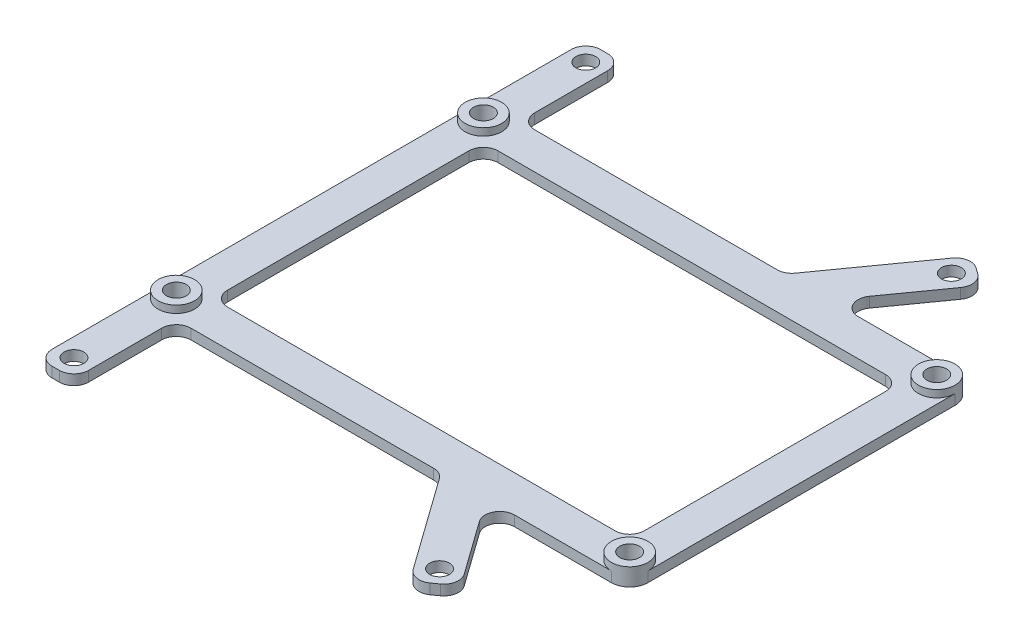
SolidWorks part; units mm, degrees
ref_plane "Front Plane" through (0, 0, 0) normal (0, 0, 1) x (1, 0, 0)
ref_plane "Top Plane" through (0, 0, 0) normal (0, 1, 0) x (1, 0, 0)
ref_plane "Right Plane" through (0, 0, 0) normal (1, 0, 0) x (0, 0, -1)
sketch "Sketch1" plane through (0, 0, 0) normal (0, 1, 0) x (1, 0, 0)
  line L0 (6, 0) -> (0, 0) construction
  line L1 (-25, -35) -> (25, -35) construction
  line L2 (-25, -35) -> (-25, 35) construction
  line L3 (-25, 35) -> (25, 35) construction
  line L4 (25, -35) -> (25, 35) construction
  line L5 (-25, -35) -> (25, 35) construction
  line L6 (-25, 35) -> (25, -35) construction
  line L7 (-25, -21) -> (37, -21) construction
  line L8 (-25, -21) -> (-25, 21) construction
  line L9 (-25, 21) -> (37, 21) construction
  line L10 (37, -21) -> (37, 21) construction
  line L11 (-25, -21) -> (37, 21) construction
  line L12 (-25, 21) -> (37, -21) construction
  circle A0 centre (-25, 35) radius 1.35
  circle A1 centre (25, 35) radius 1.35
  circle A2 centre (25, -35) radius 1.35
  circle A3 centre (-25, -35) radius 1.35
  circle A4 centre (-25, 21) radius 1.35
  circle A5 centre (37, 21) radius 1.35
  circle A6 centre (37, -21) radius 1.35
  circle A7 centre (-25, -21) radius 1.35
  point P0 (0, 0)
  point P10 (6, 0)
  dimension "D1" = 2.7
  dimension "D6" = 2.7
  dimension "D2" = 70
  dimension "D3" = 50
  dimension "D4" = 42
  dimension "D5" = 62
  dimension "D7" = 6
sketch "Sketch2" plane through (0, 0, 0) normal (0, 1, 0) x (1, 0, 0)
  line L0 (0, 0) -> (50000, 0) construction
  line L1 (-27.5, -37.5) -> (-27.5, 37.5)
  line L2 (-27.5, 37.5) -> (-22.5, 37.5)
  line L3 (-22.5, 37.5) -> (-22.5, 23.5)
  line L4 (-22.5, 23.5) -> (13.7135, 23.5)
  line L5 (13.7135, 23.5) -> (24.4188, 38.4874)
  line L6 (24.4188, 38.4874) -> (28.4874, 35.5812)
  line L7 (28.4874, 35.5812) -> (19.858, 23.5)
  line L8 (19.858, 23.5) -> (39.5, 23.5)
  line L9 (39.5, 23.5) -> (39.5, -23.5)
  line L10 (34.5, -18.5) -> (34.5, 18.5)
  line L11 (34.5, 18.5) -> (-22.5, 18.5)
  line L12 (-22.5, 18.5) -> (-22.5, -18.5)
  line L13 (-25, -35) -> (-25, 35) construction
  line L14 (-25, 21) -> (37, 21) construction
  line L15 (37, -21) -> (37, 21) construction
  line L16 (-25, -35) -> (25, 35) construction
  line L17 (34.5, -18.5) -> (-22.5, -18.5)
  line L18 (19.858, -23.5) -> (39.5, -23.5)
  line L19 (28.4874, -35.5812) -> (19.858, -23.5)
  line L20 (24.4188, -38.4874) -> (28.4874, -35.5812)
  line L21 (13.7135, -23.5) -> (24.4188, -38.4874)
  line L22 (-22.5, -23.5) -> (13.7135, -23.5)
  line L23 (-22.5, -37.5) -> (-22.5, -23.5)
  line L24 (-27.5, -37.5) -> (-22.5, -37.5)
  point P28 (39.5, 0)
  point P29 (34.5, 0)
  point P30 (-22.5, 0)
  point P31 (-27.5, 0)
  dimension "D1" = 2.5
  dimension "D2" = 2.5
  dimension "D3" = 2.5
  dimension "D4" = 2.5
  dimension "D5" = 2.5
  dimension "D6" = 2.5
  dimension "D7" = 2.5
  dimension "D8" = 2.5
  dimension "D9" = 2.5
  dimension "D10" = 2.5
extrude "Boss-Extrude1" add sketch "Sketch2" along normal blind 1.4
extrude "Cut-Extrude2" cut sketch "Sketch1" along normal through all
fillet "Fillet1" radius 2 8 edges at (28.4874, 0.7, 35.5812) (24.4188, 0.7, 38.4874) (-22.5, 0.7, 37.5) (-27.5, 0.7, 37.5) (28.4874, 0.7, -35.5812) (24.4188, 0.7, -38.4874) (-22.5, 0.7, -37.5) (-27.5, 0.7, -37.5)
fillet "Fillet2" radius 2 10 edges at (-22.5, 0.7, -23.5) (34.5, 0.7, -18.5) (34.5, 0.7, 18.5) (13.7135, 0.7, -23.5) (19.858, 0.7, -23.5) (-22.5, 0.7, 18.5) (-22.5, 0.7, -18.5) (-22.5, 0.7, 23.5) (13.7135, 0.7, 23.5) (19.858, 0.7, 23.5)
sketch "Sketch4" plane through (0, 1.4, 0) normal (0, 1, 0) x (1, 0, 0)
  line L0 (39.5, -23.5) -> (39.5, 23.5) construction
  circle A0 centre (37, 21) radius 2.5
  circle A1 centre (37, -21) radius 2.5
  circle A2 centre (-25, -21) radius 2.5
  circle A3 centre (-25, 21) radius 2.5
  circle A4 centre (37, 21) radius 1.35 construction
  circle A5 centre (37, -21) radius 1.35 construction
  circle A6 centre (-25, -21) radius 1.35 construction
  circle A7 centre (-25, 21) radius 1.35 construction
  circle A8 centre (37, 21) radius 1.35
  circle A9 centre (37, -21) radius 1.35
  circle A10 centre (-25, -21) radius 1.35
  circle A11 centre (-25, 21) radius 1.35
extrude "Boss-Extrude2" add sketch "Sketch4" along normal blind 1
sketch "Sketch5" plane through (0, 1.4, 0) normal (0, 1, 0) x (1, 0, 0)
  line L0 (37, -23.5) -> (39.5, -23.5)
  line L1 (39.5, -23.5) -> (39.5, -21)
  line L2 (39.5, 21) -> (39.5, 23.5)
  line L3 (39.5, 23.5) -> (37, 23.5)
  arc A0 (37, -23.5) -> (39.5, -21) centre (37, -21) ccw construction
  arc A1 (39.5, 21) -> (37, 23.5) centre (37, 21) ccw construction
  arc A2 (37, -23.5) -> (39.5, -21) centre (37, -21) ccw
  arc A3 (39.5, 21) -> (37, 23.5) centre (37, 21) ccw
extrude "Cut-Extrude3" cut sketch "Sketch5" against normal through all
